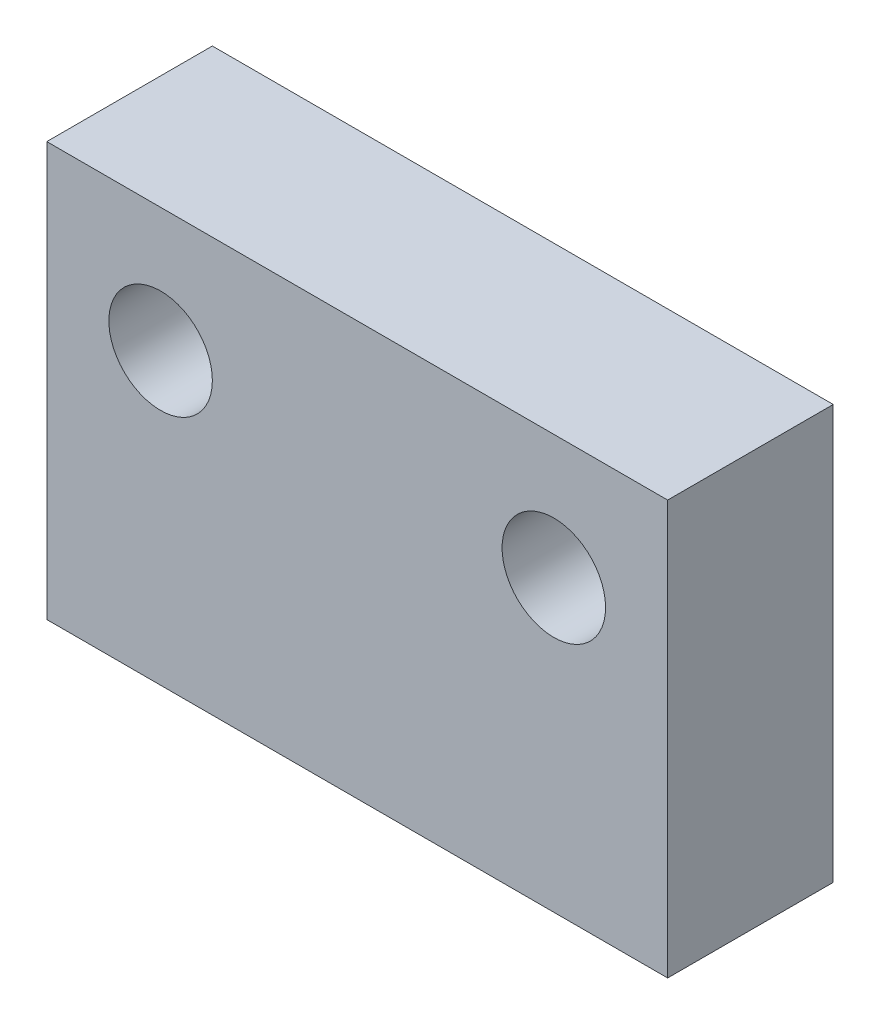
SolidWorks part; units mm, degrees
ref_plane "前视基准面" through (0, 0, 0) normal (0, 0, 1) x (1, 0, 0)
ref_plane "上视基准面" through (0, 0, 0) normal (0, 1, 0) x (1, 0, 0)
ref_plane "右视基准面" through (0, 0, 0) normal (1, 0, 0) x (0, 0, -1)
sketch "草图1" plane through (0, 0, 0) normal (0, 0, 1) x (1, 0, 0)
  line L0 (0, 0) -> (0, 3.8085) construction
  line L1 (-7.5, -5) -> (7.5, -5)
  line L2 (-7.5, -5) -> (-7.5, 5)
  line L3 (-7.5, 5) -> (7.5, 5)
  line L4 (7.5, -5) -> (7.5, 5)
  line L5 (-7.5, -5) -> (7.5, 5) construction
  line L6 (-7.5, 5) -> (7.5, -5) construction
  circle A0 centre (-4.75, 2) radius 1.25
  circle A1 centre (4.75, 2) radius 1.25
  point P0 (0, 0)
  dimension "D3" = 9.5
  dimension "D4" = 2.5
  dimension "D5" = 3
  dimension "D1" = 15
  dimension "D2" = 10
extrude "凸台-拉伸1" add sketch "草图1" along normal blind 4
